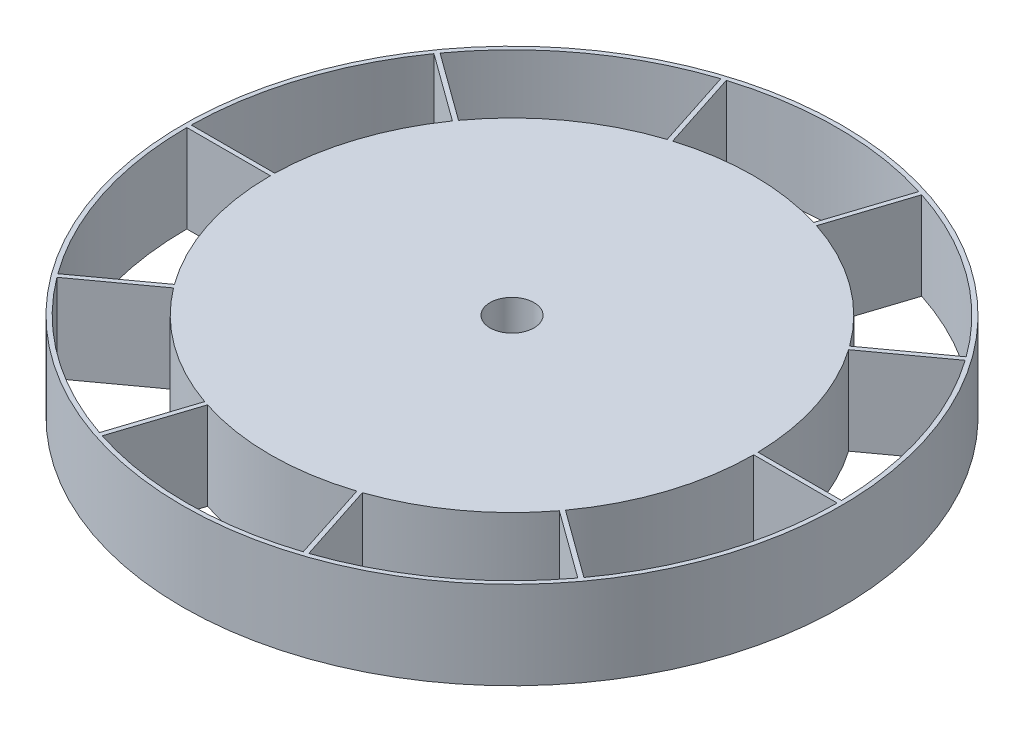
SolidWorks part; units mm, degrees
ref_plane "Front Plane" through (0, 0, 0) normal (0, 0, 1) x (1, 0, 0)
ref_plane "Top Plane" through (0, 0, 0) normal (0, 1, 0) x (1, 0, 0)
ref_plane "Right Plane" through (0, 0, 0) normal (1, 0, 0) x (0, 0, -1)
sketch "Sketch1" plane through (0, 0, 0) normal (0, 1, 0) x (1, 0, 0)
  circle A0 centre (0, 0) radius 75
  circle A1 centre (0, 0) radius 74
extrude "Boss-Extrude1" add sketch "Sketch1" along normal blind 20
sketch "Sketch2" plane through (0, 0, 0) normal (0, 1, 0) x (1, 0, 0)
  circle A0 centre (0, 0) radius 55
extrude "Boss-Extrude2" add sketch "Sketch2" along normal blind 20 separate body
sketch "Sketch3" plane through (0, 0, 0) normal (0, 1, 0) x (1, 0, 0)
  line L0 (-74, 0) -> (-1.7013, 0)
  line L1 (-22.8673, 70.3782) -> (-0.5257, 1.618)
  line L2 (59.8673, 43.4961) -> (1.3764, 1)
  line L3 (59.8673, -43.4961) -> (1.3764, -1)
  line L4 (-22.8673, -70.3782) -> (-0.5257, -1.618)
  line L5 (-73.9932, 1) -> (-3.0777, 1)
  line L6 (-21.9141, 70.6808) -> (0, 3.2361)
  line L7 (60.4496, 42.6831) -> (3.0777, 1)
  line L8 (59.274, -44.3012) -> (1.9021, -2.618)
  line L9 (-23.8162, -70.0627) -> (-1.9021, -2.618)
  line L10 (-106.4225, 1) -> (114.9455, 1) construction
  line L11 (-106.4225, 0) -> (114.9455, 0) construction
  line L12 (0.5257, 1.618) -> (0.7265, 1)
  line L13 (0, 3.2361) -> (21.9141, 70.6808)
  line L14 (-0.7265, 1) -> (-0.5257, 1.618)
  line L15 (-1.3764, -1) -> (-1.1756, -0.382)
  line L16 (-1.9021, -2.618) -> (-59.274, -44.3012)
  line L17 (0.5257, -1.618) -> (0, -1.2361)
  line L18 (1.9021, -2.618) -> (23.8162, -70.0627)
  line L19 (1.7013, 0) -> (1.1756, -0.382)
  line L20 (3.0777, 1) -> (73.9932, 1)
  line L23 (0.7265, 1) -> (1.3764, 1)
  line L24 (0.5257, 1.618) -> (22.8673, 70.3782)
  line L27 (-1.3764, 1) -> (-59.8673, 43.4961)
  line L28 (-1.3764, 1) -> (-0.7265, 1)
  line L29 (-3.0777, 1) -> (-60.4496, 42.6831)
  line L31 (-1.1756, -0.382) -> (-1.7013, 0)
  line L32 (-1.3764, -1) -> (-59.8673, -43.4961)
  line L34 (0, -1.2361) -> (-0.5257, -1.618)
  line L35 (0.5257, -1.618) -> (22.8673, -70.3782)
  line L38 (1.1756, -0.382) -> (1.3764, -1)
  line L39 (1.7013, 0) -> (74, 0)
  arc A0 (60.4496, 42.6831) -> (59.8673, 43.4961) centre (0, 0) ccw
  arc A1 (22.8673, 70.3782) -> (21.9141, 70.6808) centre (0, 0) ccw
  arc A2 (-21.9141, 70.6808) -> (-22.8673, 70.3782) centre (0, 0) ccw
  arc A3 (-59.8673, 43.4961) -> (-60.4496, 42.6831) centre (0, 0) ccw
  arc A4 (-73.9932, 1) -> (-74, 0) centre (0, 0) ccw
  arc A5 (-59.8673, -43.4961) -> (-59.274, -44.3012) centre (0, 0) ccw
  arc A6 (-23.8162, -70.0627) -> (-22.8673, -70.3782) centre (0, 0) ccw
  arc A7 (22.8673, -70.3782) -> (23.8162, -70.0627) centre (0, 0) ccw
  arc A8 (59.274, -44.3012) -> (59.8673, -43.4961) centre (0, 0) ccw
  arc A9 (74, 0) -> (73.9932, 1) centre (0, 0) ccw
  point P14 (0, 0)
  point P24 (0, 0)
  dimension "D2" = 1
  dimension "D1" = 5
  dimension "D3" = 5
extrude "Boss-Extrude3" add sketch "Sketch3" along normal blind 20
sketch "Sketch4" plane through (0, 0, 0) normal (0, 1, 0) x (1, 0, 0)
  circle A1 centre (0, 0) radius 52
extrude "Cut-Extrude3" cut sketch "Sketch4" along normal blind 10
sketch "Sketch5" plane through (0, 0, 0) normal (0, 1, 0) x (1, 0, 0)
  circle A0 centre (0, 0) radius 5
extrude "Cut-Extrude4" cut sketch "Sketch5" along normal through all
